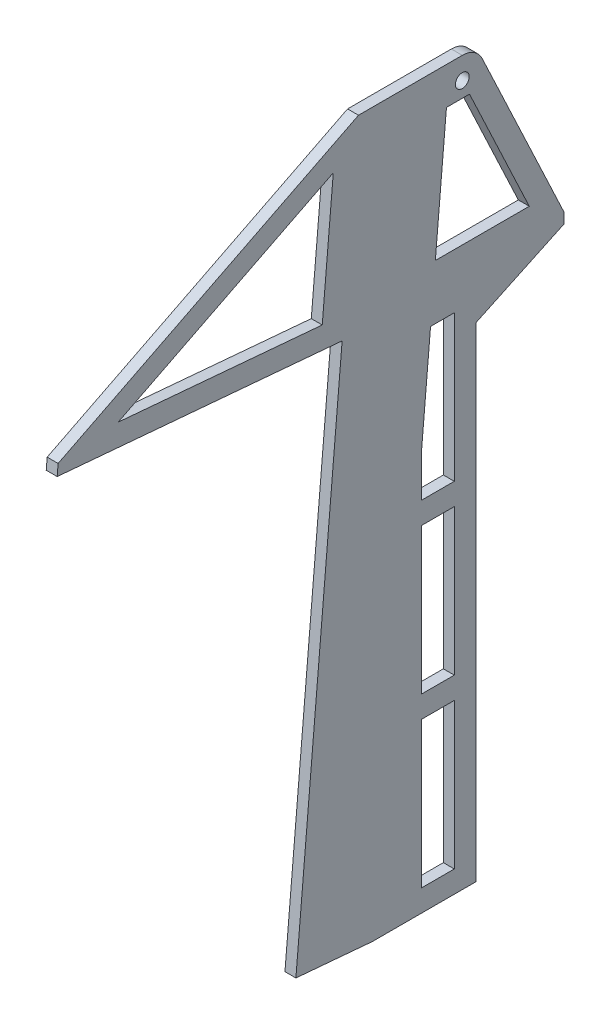
SolidWorks part; units mm, degrees
ref_plane "Front Plane" through (0, 0, 0) normal (0, 0, 1) x (1, 0, 0)
ref_plane "Top Plane" through (0, 0, 0) normal (0, 1, 0) x (1, 0, 0)
ref_plane "Right Plane" through (0, 0, 0) normal (1, 0, 0) x (0, 0, -1)
sketch "Sketch1" plane through (0, 0, 0) normal (1, 0, 0) x (0, 0, -1)
  line L0 (0, 0) -> (36.6665, 419.1) construction
  line L1 (36.6665, 419.1) -> (155.7226, 419.1) construction
  line L2 (155.7226, 419.1) -> (155.7226, 0) construction
  line L3 (155.7226, 0) -> (0, 0) construction
  line L4 (155.7226, -1000) -> (155.7226, 49000) construction
  line L5 (1.8042, 20.6221) -> (36.6665, 419.1) construction
  line L6 (1.8042, 20.6221) -> (41.652, 17.1359) construction
  line L7 (36.6665, 419.1) -> (76.5143, 415.6138) construction
  line L8 (41.652, 17.1359) -> (76.5143, 415.6138) construction
  line L9 (60.4726, -1000) -> (60.4726, 49000) construction
  line L10 (-52.7184, 317.5) -> (-128.6284, 324.1413) construction
  line L11 (-30.1965, 414.3375) -> (36.6601, 414.3375) construction
  line L12 (-1162.1335, 304.8) -> (48837.8665, 304.8) construction
  line L13 (-130.0274, 292.1) -> (-53.8274, 292.1) construction
  line L14 (-128.6284, 324.1413) -> (-53.8274, 292.1) construction
  line L15 (-52.7184, 317.5) -> (-130.0274, 292.1) construction
  line L16 (36.6601, 338.1375) -> (-30.1965, 338.1375) construction
  line L17 (-138.1172, 324.9714) -> (27.1662, 310.511)
  line L18 (-138.1172, 324.9714) -> (-137.5638, 331.2973)
  line L19 (-137.5638, 331.2973) -> (36.6665, 419.1)
  line L20 (36.6665, 419.1) -> (104.9226, 419.1)
  line L21 (104.9226, 419.1) -> (104.9226, 0) construction
  line L22 (27.1662, 310.511) -> (0.3389, 3.8741)
  line L23 (0.3389, 3.8741) -> (44.6198, 0)
  line L24 (44.6198, 0) -> (104.9226, 0)
  line L25 (104.9226, 419.1) -> (155.7226, 311.15)
  line L26 (155.7226, 311.15) -> (155.7226, 304.8)
  line L27 (155.7226, 304.8) -> (104.9226, 280.8941)
  line L28 (104.9226, 280.8941) -> (104.9226, 0)
  arc A0 (-128.6284, 324.1413) -> (-30.1965, 414.3375) centre (-30.1965, 315.5296) cw construction
  arc A1 (69.9976, 304.8) -> (36.6601, 338.1375) centre (36.6601, 304.8) ccw construction
  arc A2 (146.1976, 304.8) -> (36.6601, 414.3375) centre (36.6601, 304.8) ccw construction
  arc A3 (-52.7184, 317.5) -> (-30.1965, 338.1375) centre (-30.1965, 315.5296) cw construction
  point P7 (54.1226, 400.05)
  point P17 (146.1976, 304.8)
  point P18 (69.9976, 304.8)
  dimension "D9" = 9.525
  dimension "D14" = 25.4
  dimension "D1" = 419.1
  dimension "D2" = 101.6
  dimension "D3" = 19.05
  dimension "D4" = 19.05
  dimension "D5" = 85
  dimension "D6" = 40
  dimension "D7" = 400
  dimension "D8" = 95.25
  dimension "D10" = 9.525
  dimension "D11" = 114.3
  dimension "D12" = 76.2
  dimension "D13" = 9.525
  dimension "D15" = 127
  dimension "D16" = 9.525
  dimension "D17" = 209.55
  dimension "D18" = 6.35
  dimension "D19" = 50.8
  dimension "D20" = 44.45
  dimension "D21" = 6.35
extrude "Boss-Extrude1" add sketch "Sketch1" along normal blind 6.35
sketch "Sketch2" plane through (6.35, 0, 0) normal (1, 0, 0) x (0, 0, -1)
  line L0 (-102.7404, 334.6249) -> (22.0284, 397.5017)
  line L1 (22.0284, 397.5017) -> (15.6214, 324.2696)
  line L2 (15.6214, 324.2696) -> (-102.7404, 334.6249)
  line L3 (-138.1172, 324.9714) -> (27.1662, 310.511) construction
  line L4 (-137.5638, 331.2973) -> (36.6665, 419.1) construction
  line L5 (27.1662, 310.511) -> (0.3389, 3.8741) construction
  line L6 (87.6782, 397.5017) -> (81.2345, 323.85)
  line L7 (78.4567, 292.1) -> (73.1726, 231.702)
  line L8 (73.1726, 231.702) -> (73.1726, 207.4333)
  line L9 (92.2226, 207.4333) -> (92.2226, 292.1)
  line L10 (92.2226, 292.1) -> (78.4567, 292.1)
  line L11 (92.2226, 194.7333) -> (92.2226, 110.0667)
  line L12 (92.2226, 97.3667) -> (92.2226, 12.7)
  line L13 (44.6198, 0) -> (104.9226, 0) construction
  line L14 (73.1726, 12.7) -> (73.1726, 97.3667)
  line L15 (73.1726, 97.3667) -> (92.2226, 97.3667)
  line L17 (92.2226, 12.7) -> (73.1726, 12.7)
  line L18 (60.4726, -201000) -> (60.4726, 249000) construction
  line L19 (81.2345, 323.85) -> (135.7102, 323.85)
  line L20 (135.7102, 323.85) -> (101.0506, 397.5017)
  line L21 (101.0506, 397.5017) -> (87.6782, 397.5017)
  line L23 (104.9226, 419.1) -> (155.7226, 311.15) construction
  line L26 (41.652, 17.1359) -> (76.5143, 415.6138) construction
  line L27 (92.2226, 110.0667) -> (73.1726, 110.0667)
  line L28 (-201162.1335, 304.8) -> (248837.8665, 304.8) construction
  line L29 (104.9226, 280.8941) -> (104.9226, 0) construction
  line L32 (73.1726, 110.0667) -> (73.1726, 194.7333)
  line L33 (73.1726, 194.7333) -> (92.2226, 194.7333)
  line L34 (73.1726, 207.4333) -> (92.2226, 207.4333)
  dimension "D1" = 12.7
  dimension "D2" = 12.7
  dimension "D3" = 12.7
  dimension "D5" = 12.7
  dimension "D6" = 12.7
  dimension "D7" = 12.7
  dimension "D8" = 12.7
  dimension "D9" = 12.7
  dimension "D10" = 12.7
  dimension "D11" = 12.7
  dimension "D12" = 12.7
  dimension "D13" = 12.7
extrude "Cut-Extrude4" cut sketch "Sketch2" against normal through all
fillet "Fillet1" radius 12.7 1 edges at (3.175, 419.1, -104.9226)
sketch "Sketch3" plane through (6.35, 0, 0) normal (1, 0, 0) x (0, 0, -1)
  circle A0 centre (96.8631, 406.4) radius 4
  dimension "D1" = 8
extrude "Cut-Extrude5" cut sketch "Sketch3" against normal through all
